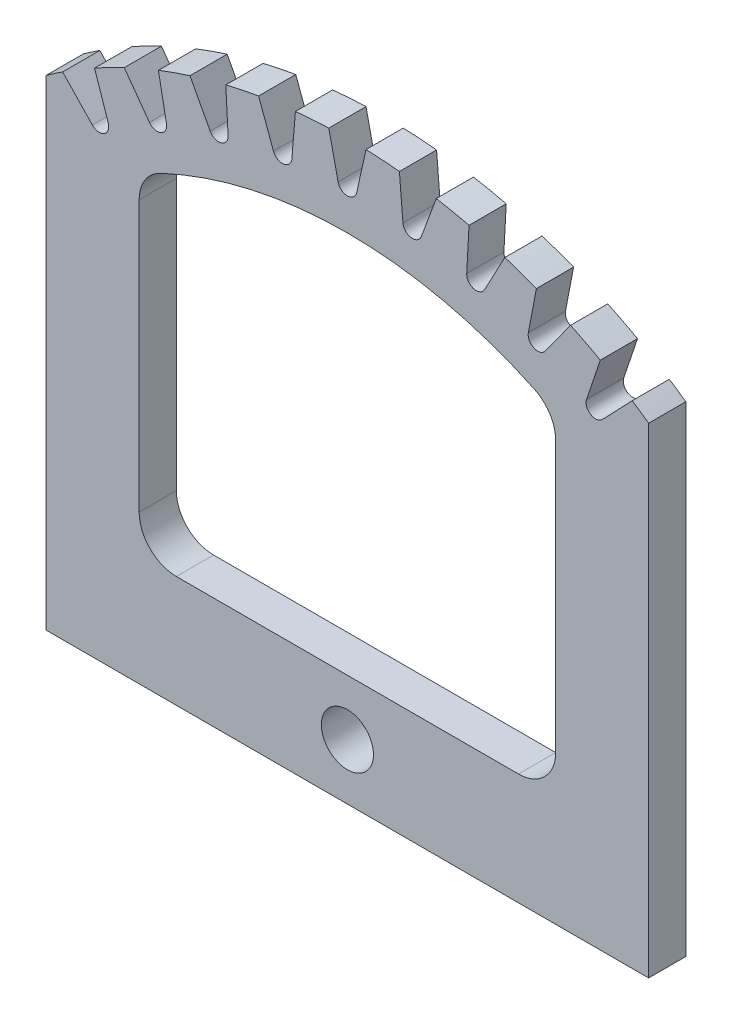
SolidWorks part; units mm, degrees
material "Acier non allié"
ref_plane "Plan de face" through (0, 0, 0) normal (0, 0, 1) x (1, 0, 0)
ref_plane "Plan de dessus" through (0, 0, 0) normal (0, 1, 0) x (1, 0, 0)
ref_plane "Plan de droite" through (0, 0, 0) normal (1, 0, 0) x (0, 0, -1)
sketch "Esquisse1" plane through (0, 0, 0) normal (0, 0, 1) x (1, 0, 0)
  line L0 (-140, 0) -> (0, 0) construction
  line L1 (0, 0) -> (140, 0) construction
  line L2 (-81, 114.1884) -> (-81, -15)
  line L3 (68.5975, 108.8454) -> (76.564, 117.209)
  line L4 (64.3165, 111.4286) -> (68.0019, 122.3754)
  line L5 (60.631, 100.4818) -> (72.3291, 119.8687) construction
  line L6 (53.2384, 117.1265) -> (59.9999, 126.4911)
  line L7 (48.6472, 119.1066) -> (50.8175, 130.4514)
  line L8 (36.9, 123.2531) -> (42.3322, 133.4466)
  line L9 (32.0831, 124.5938) -> (32.6984, 136.1279)
  line L10 (19.8829, 127.1126) -> (23.8858, 137.9473)
  line L11 (14.9288, 127.7891) -> (13.9777, 139.3005)
  line L12 (2.5, 128.6339) -> (5, 139.9107)
  line L13 (-2.5, 128.6339) -> (-5, 139.9107)
  line L14 (-14.9288, 127.7891) -> (-13.9777, 139.3005)
  line L15 (-19.8829, 127.1126) -> (-23.8858, 137.9473)
  line L16 (-32.0831, 124.5938) -> (-32.6984, 136.1279)
  line L17 (-36.9, 123.2531) -> (-42.3322, 133.4466)
  line L18 (-48.6472, 119.1066) -> (-50.8175, 130.4514)
  line L19 (-53.2384, 117.1265) -> (-59.9999, 126.4911)
  line L20 (-64.3165, 111.4286) -> (-68.0019, 122.3754)
  line L21 (-68.5975, 108.8454) -> (-76.564, 117.209)
  line L22 (81, -15) -> (-81, -15)
  line L23 (-56, 97.7139) -> (-56, 25)
  line L24 (-46, 15) -> (46, 15)
  line L25 (56, 25) -> (56, 97.7139)
  line L26 (81, -15) -> (81, 114.1884)
  line L27 (0, 15) -> (0, -15) construction
  arc A1 (118, 0) -> (-118, 0) centre (0, 0) ccw construction
  arc A2 (76.564, 117.209) -> (68.0019, 122.3754) centre (0, 0) ccw
  arc A3 (53.2384, 117.1265) -> (48.6472, 119.1066) centre (51.1623, 118.6255) cw
  arc A4 (68.0019, 122.3754) -> (59.9999, 126.4911) centre (0, 0) ccw
  arc A5 (76.564, 117.209) -> (81, 114.1884) centre (0, 0) cw
  arc A6 (140, 0) -> (-140, 0) centre (0, 0) ccw construction
  arc A7 (68.5975, 108.8454) -> (64.3165, 111.4286) centre (66.7433, 110.6115) cw
  arc A8 (50.8175, 130.4514) -> (42.3322, 133.4466) centre (0, 0) ccw
  arc A9 (36.9, 123.2531) -> (32.0831, 124.5938) centre (34.6402, 124.4574) cw
  arc A10 (32.6984, 136.1279) -> (23.8858, 137.9473) centre (0, 0) ccw
  arc A11 (19.8829, 127.1126) -> (14.9288, 127.7891) centre (17.4809, 128) cw
  arc A12 (13.9777, 139.3005) -> (5, 139.9107) centre (0, 0) ccw
  arc A13 (2.5, 128.6339) -> (-2.5, 128.6339) centre (0, 129.1882) cw
  arc A14 (-5, 139.9107) -> (-13.9777, 139.3005) centre (0, 0) ccw
  arc A15 (-14.9288, 127.7891) -> (-19.8829, 127.1126) centre (-17.4809, 128) cw
  arc A16 (-23.8858, 137.9473) -> (-32.6984, 136.1279) centre (0, 0) ccw
  arc A17 (-32.0831, 124.5938) -> (-36.9, 123.2531) centre (-34.6402, 124.4574) cw
  arc A18 (-42.3322, 133.4466) -> (-50.8175, 130.4514) centre (0, 0) ccw
  arc A19 (-48.6472, 119.1066) -> (-53.2384, 117.1265) centre (-51.1623, 118.6255) cw
  arc A20 (-59.9999, 126.4911) -> (-68.0019, 122.3754) centre (0, 0) ccw
  arc A21 (-64.3165, 111.4286) -> (-68.5975, 108.8454) centre (-66.7433, 110.6115) cw
  circle A22 centre (0, 0) radius 7
  arc A23 (-56, 25) -> (-46, 15) centre (-46, 25) ccw
  arc A24 (-76.564, 117.209) -> (-81, 114.1884) centre (0, 0) ccw
  arc A25 (50.2593, 106.7614) -> (-50.2593, 106.7614) centre (0, 0) ccw
  arc A26 (46, 15) -> (56, 25) centre (46, 25) ccw
  arc A27 (56, 97.7139) -> (50.2593, 106.7614) centre (46, 97.7139) ccw
  arc A28 (-56, 97.7139) -> (-50.2593, 106.7614) centre (-46, 97.7139) cw
  point P72 (56, 103.8653)
  point P73 (0, 0)
  point P76 (-56, 103.8653)
  dimension "D1" = 140
  dimension "D2" = 22
  dimension "D4" = 25
  dimension "D5" = 162
  dimension "D6" = 5
  dimension "D10" = 14
  dimension "D11" = 58.893
  dimension "D14" = 10
  dimension "D7" = 10
  dimension "D8" = 9
  dimension "D12" = 30
  dimension "D13" = 25
  dimension "D16" = 81
  dimension "D9" = 9
extrude "Boss.-Extru.2" add sketch "Esquisse1" along normal mid plane 10
